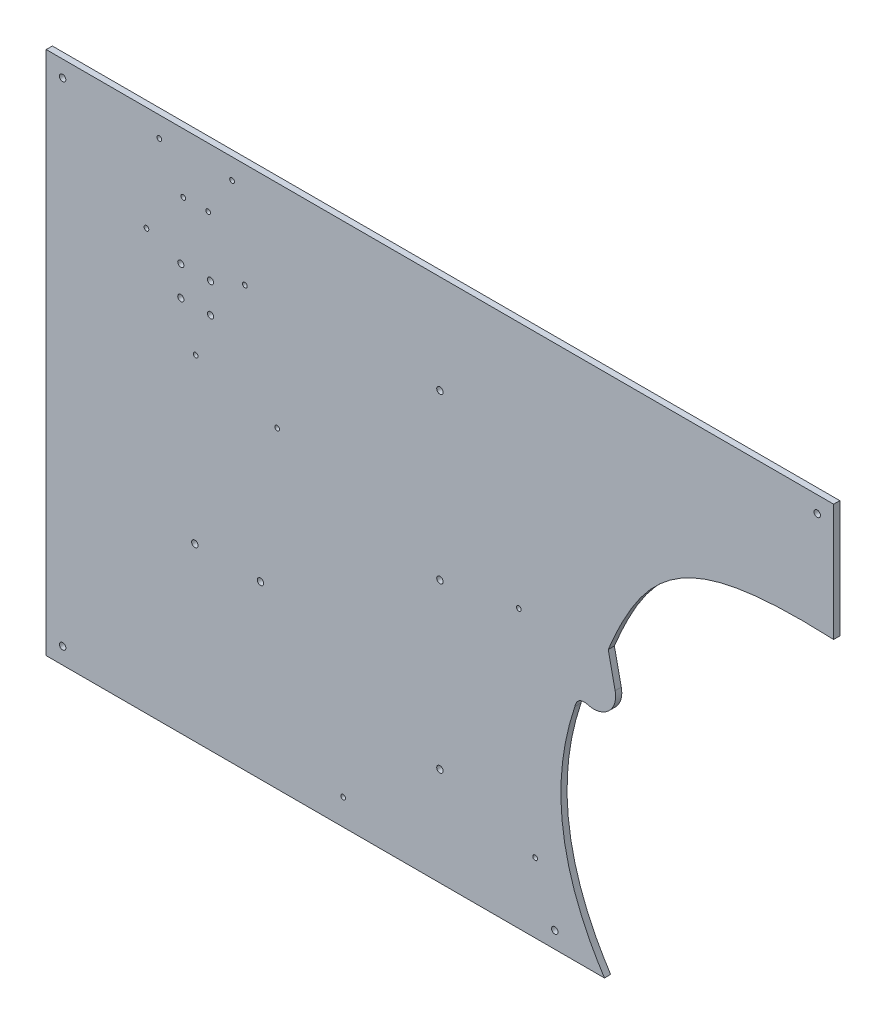
SolidWorks part; units mm, degrees
material "Acrylic (Medium-high impact)"
ref_plane "Front Plane" through (0, 0, 0) normal (0, 0, 1) x (1, 0, 0)
ref_plane "Top Plane" through (0, 0, 0) normal (0, 1, 0) x (1, 0, 0)
ref_plane "Right Plane" through (0, 0, 0) normal (1, 0, 0) x (0, 0, -1)
sketch "Sketch1" plane through (0, 0, 0) normal (0, 0, 1) x (1, 0, 0)
  line L1 (0, 0) -> (609.6, 0)
  line L2 (0, 0) -> (0, 406.4)
  line L3 (0, 406.4) -> (609.6, 406.4)
  line L4 (609.6, 0) -> (609.6, 406.4)
  dimension "D1" = 609.6
  dimension "D2" = 406.4
extrude "Boss-Extrude1" add sketch "Sketch1" along normal blind 4.7625
hole_wizard "#10 Clearance Hole1" positions "Sketch5" profile "Sketch6" hole size "#10" standard "ANSI Inch"
sketch "Sketch5" plane through (0, 0, 4.7625) normal (0, 0, 1) x (1, 0, 0)
  line L0 (0, 406.4) -> (609.6, 0) construction
  line L3 (12.7, 12.7) -> (596.9, 12.7)
  line L4 (12.7, 12.7) -> (12.7, 393.7)
  line L5 (12.7, 393.7) -> (596.9, 393.7)
  line L6 (596.9, 12.7) -> (596.9, 393.7)
  line L7 (12.7, 12.7) -> (596.9, 393.7) construction
  line L8 (12.7, 393.7) -> (596.9, 12.7) construction
  line L9 (609.6, 406.4) -> (0, 406.4) construction
  line L10 (0, 406.4) -> (0, 0) construction
  line L11 (304.8, 203.2) -> (304.8, 330.2) construction
  line L13 (304.8, 203.2) -> (304.8, 76.2) construction
  point P6 (304.8, 203.2)
  point P7 (596.9, 393.7)
  point P114 (12.7, 12.7)
  point P115 (12.7, 393.7)
  point P116 (596.9, 12.7)
  point P132 (304.8, 330.2)
  point P136 (304.8, 76.2)
  point P139 (393.7, 12.7)
  dimension "D1" = 12.7
  dimension "D2" = 12.7
  dimension "D3" = 127
  dimension "D4" = 203.2
sketch "Sketch6" plane through (393.7, 12.7, 4.7625) normal (1, 0, 0) x (0, -1, 0)
  line L0 (0, 0) -> (0, 11.6557)
  line L1 (0, 11.6557) -> (2.4892, 10.16)
  line L2 (2.4892, 10.16) -> (2.4892, 0)
  line L5 (2.4892, 0) -> (0, 0)
  line L10 (0, 11.6557) -> (-2.4892, 10.16) construction
  line L11 (0, -6.35) -> (0, 107.95) construction
  dimension "Hole Dia." = 4.9784
  dimension "Hole Depth" = 10.16
  dimension "Drill Angle" = 118
hole_wizard "#6 Clearance Hole1" positions "Sketch7" profile "Sketch8" hole size "#6" standard "ANSI Inch"
sketch "Sketch7" plane through (0, 0, 4.7625) normal (0, 0, 1) x (1, 0, 0)
  point P33 (153.8, 325.397)
  point P36 (115.7, 259.4059)
  point P39 (77.6, 325.397)
  point P42 (178.7486, 241.9865)
  point P45 (365.913, 214.6035)
  point P48 (378.5146, 53.8049)
  point P51 (229.8814, 20.1311)
  point P54 (87.5115, 390.5394)
  point P57 (106.048, 360.365)
  point P60 (125.352, 360.365)
  point P63 (143.8885, 390.5394)
sketch "Sketch8" plane through (153.8, 325.397, 4.7625) normal (1, 0, 0) x (0, -1, 0)
  line L0 (0, 0) -> (0, 11.2589)
  line L1 (0, 11.2589) -> (1.8288, 10.16)
  line L2 (1.8288, 10.16) -> (1.8288, 0)
  line L5 (1.8288, 0) -> (0, 0)
  line L10 (0, 11.2589) -> (-1.8288, 10.16) construction
  line L11 (0, -6.35) -> (0, 107.95) construction
  dimension "Hole Dia." = 3.6576
  dimension "Hole Depth" = 10.16
  dimension "Drill Angle" = 118
hole_wizard "1/4 Clearance Hole1" [suppressed] positions "Sketch9" profile "Sketch10" hole size "1/4" standard "ANSI Inch"
sketch "Sketch9" plane through (0, 0, 6.35) normal (0, 0, 1) x (1, 0, 0)
  line L10 (304.8, 406.4) -> (304.8, 0) construction
  line L11 (609.6, 406.4) -> (0, 406.4) construction
  line L12 (0, 0) -> (609.6, 0) construction
  line L15 (31.75, 31.75) -> (577.85, 31.75)
  line L16 (31.75, 31.75) -> (31.75, 374.65)
  line L17 (31.75, 374.65) -> (577.85, 374.65)
  line L18 (577.85, 31.75) -> (577.85, 374.65)
  line L19 (31.75, 31.75) -> (577.85, 374.65) construction
  line L20 (31.75, 374.65) -> (577.85, 31.75) construction
  line L21 (0, 406.4) -> (0, 0) construction
  line L22 (86.7162, 374.65) -> (86.7162, 406.4) construction
  line L24 (31.75, 331.6441) -> (0, 331.6441) construction
  point P135 (304.8, 203.2)
  point P136 (577.85, 374.65)
  point P187 (31.75, 31.75)
  point P188 (31.75, 374.65)
  point P189 (577.85, 31.75)
  dimension "D1" = 31.75
sketch "Sketch10" plane through (577.85, 31.75, 6.35) normal (1, 0, 0) x (0, -1, 0)
  line L0 (0, 0) -> (0, 12.1211)
  line L1 (0, 12.1211) -> (3.2639, 10.16)
  line L2 (3.2639, 10.16) -> (3.2639, 0)
  line L5 (3.2639, 0) -> (0, 0)
  line L10 (0, 12.1211) -> (-3.2639, 10.16) construction
  line L11 (0, -6.35) -> (0, 107.95) construction
  dimension "Hole Dia." = 6.5278
  dimension "Hole Depth" = 10.16
  dimension "Drill Angle" = 118
hole_wizard "#10 Clearance Hole2" positions "Sketch11" profile "Sketch12" hole size "#10" standard "ANSI Inch"
sketch "Sketch11" plane through (0, 0, 4.7625) normal (0, 0, 1) x (1, 0, 0)
  point P7 (165.8937, 132.5562)
  point P10 (115.0937, 132.5562)
sketch "Sketch12" plane through (165.8937, 132.5562, 4.7625) normal (1, 0, 0) x (0, -1, 0)
  line L0 (0, 0) -> (0, 11.6557)
  line L1 (0, 11.6557) -> (2.4892, 10.16)
  line L2 (2.4892, 10.16) -> (2.4892, 0)
  line L5 (2.4892, 0) -> (0, 0)
  line L10 (0, 11.6557) -> (-2.4892, 10.16) construction
  line L11 (0, -6.35) -> (0, 107.95) construction
  dimension "Hole Dia." = 4.9784
  dimension "Hole Depth" = 10.16
  dimension "Drill Angle" = 118
sketch "Sketch13" plane through (0, 0, 4.7625) normal (0, 0, 1) x (1, 0, 0)
  circle A0 centre (173.7866, 102.0811) radius 8.255
  dimension "D1" = 16.51
extrude "Cut-Extrude3" [suppressed] cut sketch "Sketch13" against normal through all
sketch "Sketch14" plane through (0, 0, 0) normal (0, 0, 1) x (1, 0, 0)
  line L5 (609.6, 315.6425) -> (609.6, 0)
  line L6 (609.6, 0) -> (432.1959, 0)
  line L7 (0, 0) -> (609.6, 0) construction
  line L16 (440.4597, 196.7472) -> (435.087, 221.6826)
  arc A2 (418.0723, 177.1306) -> (440.4597, 196.7472) centre (423.8143, 193.1607) ccw
  spline S0 degree 3 poles (435.087, 221.6826) (465.2439, 294.7904) (498.0322, 320.6412) (609.6, 315.6425) knots 0.107899 0.107899 0.107899 0.107899 1 1 1 1
  spline S1 degree 3 poles (409.2966, 170.6179) (389.3367, 111.2266) (396.9698, 54.3539) (432.1959, 0) knots 0.116937 0.116937 0.116937 0.116937 1 1 1 1
  spline S2 degree 2 poles (418.0723, 177.1306) (410.9297, 177.9535) (409.2966, 170.6179) knots 0 0 0 1 1 1
  point P25 (443.0184, 184.8726)
  dimension "D11" = 472.1307
  dimension "D1" = 17.0274
  dimension "D2" = 399.5965
  dimension "D3" = 409.2966
  dimension "D4" = 412.7536
  dimension "D5" = 418.0723
  dimension "D6" = 423.8143
  dimension "D7" = 432.1959
  dimension "D8" = 435.087
  dimension "D9" = 440.4597
  dimension "D10" = 443.0184
  dimension "D12" = 87.0998
  dimension "D13" = 170.6179
  dimension "D14" = 176.2154
  dimension "D15" = 177.1306
  dimension "D20" = 282.931
  dimension "D21" = 315.6425
extrude "Cut-Extrude6" cut sketch "Sketch14" along normal through all
sketch "Sketch17" [suppressed] plane through (0, 0, 0) normal (0, 0, 1) x (1, 0, 0)
  line L8 (609.6, 315.6425) -> (609.6, 406.4)
  line L9 (609.6, 406.4) -> (0, 406.4)
  line L16 (440.4597, 196.7472) -> (435.087, 221.6826)
  line L17 (0, 406.4) -> (0, 0)
  line L18 (0, 0) -> (432.1959, 0)
  arc A2 (418.0723, 177.1306) -> (440.4597, 196.7472) centre (423.8143, 193.1607) ccw
  spline S0 degree 3 poles (435.087, 221.6826) (465.2439, 294.7904) (498.0322, 320.6412) (609.6, 315.6425) knots 0.107899 0.107899 0.107899 0.107899 1 1 1 1
  spline S1 degree 3 poles (409.2966, 170.6179) (389.3367, 111.2266) (396.9698, 54.3539) (432.1959, 0) knots 0.116937 0.116937 0.116937 0.116937 1 1 1 1
  spline S2 degree 2 poles (418.0723, 177.1306) (410.9297, 177.9535) (409.2966, 170.6179) knots 0 0 0 1 1 1
  point P25 (443.0184, 184.8726)
  dimension "D1" = 17.0274
extrude "Cut-Extrude9" [suppressed] cut sketch "Sketch17" along normal through all
sketch "Sketch18" [suppressed] plane through (0, 0, 6.35) normal (0, 0, 1) x (1, 0, 0)
  line L0 (407.5595, 165.2304) -> (589.28, 155.7068)
  line L1 (589.28, 155.7068) -> (423.8678, 155.7068) construction
  line L2 (589.28, 155.7068) -> (589.28, 136.6568) construction
  line L3 (423.8678, 155.7068) -> (423.8678, 8.4378) construction
  line L4 (589.28, 136.6568) -> (423.8678, 127.988)
  line L5 (589.28, 136.6568) -> (423.8678, 136.6568) construction
  line L6 (609.6, 0) -> (609.6, 315.6425) construction
  line L7 (398.4678, 185.2864) -> (398.4678, -6.6736) construction
  line L8 (423.8678, 127.988) -> (423.8678, 108.938) construction
  line L9 (423.8678, 108.938) -> (589.28, 108.938) construction
  line L10 (423.8678, 108.938) -> (589.28, 100.2691)
  line L11 (589.28, 81.2191) -> (423.8678, 72.5502)
  line L12 (423.8678, 72.5502) -> (402.0815, 71.4084)
  line L13 (423.8678, 53.5002) -> (589.28, 44.8313) [skipped]
  arc A0 (589.28, 136.6568) -> (589.28, 155.7068) centre (589.28, 146.1818) ccw
  arc A1 (423.8678, 127.988) -> (423.8678, 108.938) centre (423.8678, 118.463) ccw
  arc A2 (589.28, 81.2191) -> (589.28, 100.2691) centre (589.28, 90.7441) ccw
  arc A4 (423.8678, 72.5502) -> (423.8678, 53.5002) centre (423.8678, 63.0252) ccw [skipped]
  spline S0 degree 3 poles (432.1959, 0) (396.9698, 54.3539) (389.3367, 111.2266) (409.2966, 170.6179) knots 0.116937 0.116937 0.116937 0.116937 1 1 1 1 construction
  dimension "D1" = 19.05
  dimension "D6" = 19.05
  dimension "D2" = 3
  dimension "D3" = 3
  dimension "D4" = 20.32
  dimension "D5" = 25.4
  dimension "D7" = 3
  dimension "D8" = 2
ref_plane "Plane1" [suppressed] through (407.5595, 165.2304, 6.35) normal (0.9986, -0.0523, 0) x (0, 0, -1)
sketch "Sketch19" [suppressed] plane through (407.5595, 165.2304, 6.35) normal (0.9986, -0.0523, 0) x (0, 0, -1)
  line L0 (6.35, -163.7146) -> (6.35, 5.4711) construction
  line L1 (0, -4.953) -> (6.35, -4.953)
  line L2 (0, -4.953) -> (0, 4.953)
  line L3 (0, 4.953) -> (6.35, 4.953)
  line L4 (6.35, -4.953) -> (6.35, 4.953)
  line L5 (0, 5.4711) -> (0, -163.7146) construction
  line L7 (0, 0) -> (6.35, 0) construction
  point P13 (0, 0)
  dimension "D1" = 9.906
sweep "Cut-Sweep1" [suppressed] cut profiles "Sketch19" path "Sketch18"
sketch "Sketch20" [suppressed] plane through (0, 0, 6.35) normal (0, 0, 1) x (1, 0, 0)
  line L0 (409.1259, 170.1081) -> (589.4232, 160.6591) construction
  line L1 (440.4597, 196.7472) -> (435.087, 221.6826) construction
  line L3 (409.1259, 170.1081) -> (472.7844, 166.7719)
  line L4 (440.4597, 196.7472) -> (472.7844, 166.7719)
  arc A1 (409.2966, 170.6179) -> (409.1259, 170.1081) centre (629.1234, 96.7398) ccw construction
  arc A2 (418.0723, 177.1306) -> (440.4597, 196.7472) centre (423.8143, 193.1607) ccw construction
  arc A3 (409.2966, 170.6179) -> (409.1259, 170.1081) centre (629.1234, 96.7398) ccw
  arc A4 (418.0723, 177.1306) -> (440.4597, 196.7472) centre (423.8143, 193.1607) ccw
  parabola Q1 (409.2966, 170.6179) -> (418.0723, 177.1306) focus (414.2209, 173.5612) apex (412.527, 176.0696) construction
  parabola Q2 (409.2966, 170.6179) -> (418.0723, 177.1306) focus (414.2209, 173.5612) apex (412.527, 176.0696)
  dimension "D1" = 145
extrude "Cut-Extrude10" [suppressed] cut sketch "Sketch20" against normal through all
hole_wizard "#6 Clearance Hole2" [suppressed] positions "Sketch21" profile "Sketch22" hole size "#6" standard "ANSI Inch"
sketch "Sketch21" plane through (0, 0, 6.35) normal (0, 0, 1) x (1, 0, 0)
  point P0 (589.28, 146.1818)
  point P2 (589.28, 90.7441)
  point P4 (423.8678, 118.463)
  point P6 (410.9295, 149.3596)
  point P8 (407.3718, 84.2504)
  point P10 (600.075, 120.1926)
  point P12 (480.8491, 277.5715)
  point P14 (600.075, 306.5575)
  point P16 (440.0722, 12.276)
  point P42 (478.133, 178.9044)
sketch "Sketch22" plane through (589.28, 146.1818, 6.35) normal (1, 0, 0) x (0, -1, 0)
  line L0 (0, 0) -> (0, 11.2589)
  line L1 (0, 11.2589) -> (1.8288, 10.16)
  line L2 (1.8288, 10.16) -> (1.8288, 0)
  line L5 (1.8288, 0) -> (0, 0)
  line L10 (0, 11.2589) -> (-1.8288, 10.16) construction
  line L11 (0, -6.35) -> (0, 107.95) construction
  dimension "Hole Dia." = 3.6576
  dimension "Hole Depth" = 10.16
  dimension "Drill Angle" = 118
hole_wizard "3/16 (0.1875) Diameter Hole1" positions "Sketch23" profile "Sketch24" hole size "3/16" standard "ANSI Inch"
sketch "Sketch23" plane through (0, 0, 4.7625) normal (0, 0, 1) x (1, 0, 0)
  point P0 (127.2, 314.9)
  point P3 (127.2, 291.9)
  point P6 (104.2, 291.9)
  point P9 (104.2, 314.9)
sketch "Sketch24" plane through (127.2, 314.9, 4.7625) normal (1, 0, 0) x (0, -1, 0)
  line L0 (0, 0) -> (0, 11.5908)
  line L1 (0, 11.5908) -> (2.3812, 10.16)
  line L2 (2.3812, 10.16) -> (2.3812, 0)
  line L5 (2.3812, 0) -> (0, 0)
  line L10 (0, 11.5908) -> (-2.3813, 10.16) construction
  line L11 (0, -6.35) -> (0, 107.95) construction
  dimension "Hole Dia." = 4.7625
  dimension "Hole Depth" = 10.16
  dimension "Drill Angle" = 118
equation "\"thick\" = 0.1875"
equation "\"D1@Boss-Extrude1\"=\"thick\""
